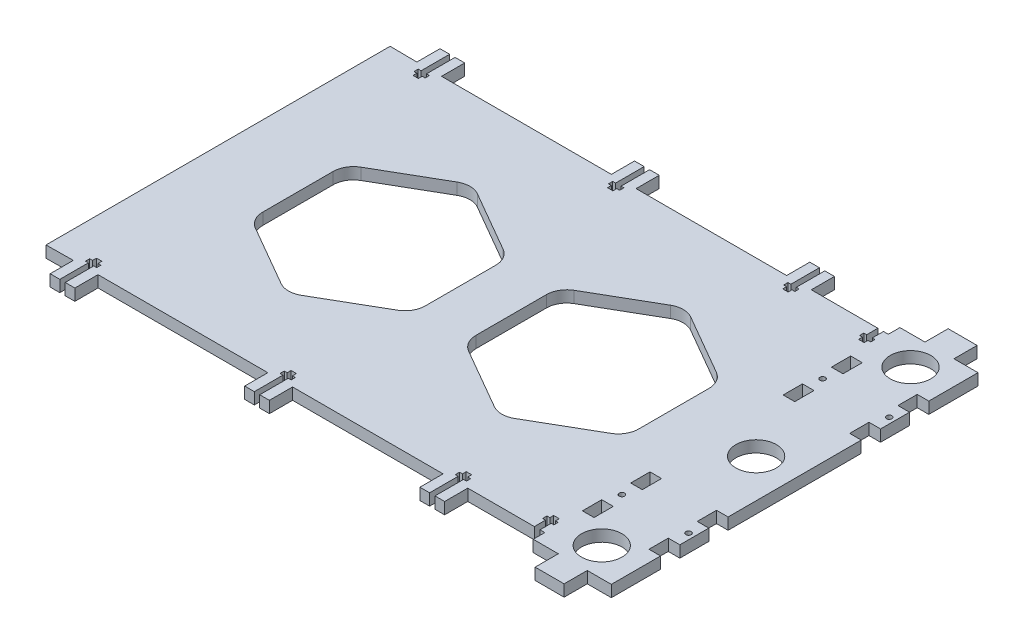
SolidWorks part; units mm, degrees
ref_plane "Спереди" through (0, 0, 0) normal (0, 0, 1) x (1, 0, 0)
ref_plane "Сверху" through (0, 0, 0) normal (0, 1, 0) x (1, 0, 0)
ref_plane "Справа" through (0, 0, 0) normal (1, 0, 0) x (0, 0, -1)
sketch "Эскиз1" plane through (0, 0, 0) normal (0, 1, 0) x (1, 0, 0)
  line L32 (-23.9169, 26.9382) -> (-55.4959, 45.1703)
  line L33 (-66.0222, 45.1703) -> (-97.6012, 26.9382)
  line L34 (-102.8643, 17.8222) -> (-102.8643, -0.4099)
  line L37 (-18.6538, -18.6421) -> (-18.6538, 17.8222)
  line L40 (91.8726, -0.4099) -> (91.8726, 17.8222)
  line L41 (86.6094, 26.9382) -> (55.0304, 45.1703)
  line L42 (44.5041, 45.1703) -> (12.9252, 26.9382)
  line L43 (7.662, 17.8222) -> (7.662, -18.6421)
  line L188 (154.5041, 128.5638) -> (154.5041, -125.2674) construction
  line L189 (175.6449, -0.4099) -> (-201.3479, -0.4099) construction
  line L190 (169.6988, 94.5901) -> (-201.3479, 94.5901) construction
  line L191 (168.2514, -95.4099) -> (-202.7953, -95.4099) construction
  line L192 (169.6988, 106.5901) -> (89.704, 106.5901) construction
  line L193 (-117.4736, -101.4099) -> (-117.4736, -89.4099)
  line L194 (108.4192, -125.2328) -> (108.4192, 116.6247) construction
  line L195 (134.5357, 79.5901) -> (134.5357, 90.0901) construction
  line L196 (134.5357, 128.5638) -> (134.5357, -125.2674) construction
  line L197 (148.5041, 128.5638) -> (148.5041, -125.2674) construction
  line L198 (169.6988, 69.0901) -> (102.787, 69.0901) construction
  line L199 (120.0357, -95.4099) -> (114.0357, -95.4099)
  line L200 (169.6988, 59.0901) -> (102.787, 59.0901) construction
  line L201 (102.787, 44.0901) -> (169.6988, 44.0901) construction
  line L202 (102.787, 34.0901) -> (169.6988, 34.0901) construction
  line L203 (-122.4736, -101.4099) -> (-117.4736, -101.4099)
  line L204 (-130.2736, -101.4099) -> (-130.2736, -89.4099)
  line L205 (-125.2736, -101.4099) -> (-130.2736, -101.4099)
  line L206 (-126.7736, -86.6099) -> (-125.2736, -86.6099)
  line L207 (154.5041, 69.0901) -> (148.5041, 69.0901)
  line L208 (148.5041, 69.0901) -> (148.5041, 59.0901)
  line L209 (148.5041, 59.0901) -> (154.5041, 59.0901)
  line L210 (154.5041, 44.0901) -> (148.5041, 44.0901)
  line L211 (148.5041, 44.0901) -> (148.5041, 34.0901)
  line L212 (148.5041, 34.0901) -> (154.5041, 34.0901)
  line L213 (151.5041, 128.5638) -> (151.5041, -125.2674) construction
  line L214 (169.6988, 51.5901) -> (102.787, 51.5901) construction
  line L215 (-126.7736, -84.4099) -> (-126.7736, -86.6099)
  line L223 (154.5041, -34.9099) -> (154.5041, 34.0901)
  line L224 (154.5041, 44.0901) -> (154.5041, 59.0901)
  line L225 (154.5041, 69.0901) -> (154.5041, 94.5901)
  line L227 (142.0357, 94.5901) -> (142.0357, 106.5901)
  line L228 (142.0357, 106.5901) -> (127.0357, 106.5901)
  line L229 (127.0357, 106.5901) -> (127.0357, 94.5901)
  line L230 (142.0357, 94.5901) -> (154.5041, 94.5901)
  line L231 (124.0357, 116.5901) -> (124.0357, -125.2674) construction
  line L232 (120.0357, 116.5901) -> (120.0357, -125.2674) construction
  line L233 (114.0357, 116.5901) -> (114.0357, -125.2674) construction
  line L234 (169.6988, 88.5901) -> (114.0357, 88.5901) construction
  line L236 (120.0357, 94.5901) -> (127.0357, 94.5901)
  line L238 (-24.4736, 100.5895) -> (-24.4736, 85.7895)
  line L239 (116.9781, 116.5901) -> (116.9781, -125.2674) construction
  line L240 (114.0357, 69.0901) -> (120.0357, 69.0901)
  line L241 (114.0357, 69.0901) -> (114.0357, 59.0901)
  line L242 (114.0357, 59.0901) -> (120.0357, 59.0901)
  line L243 (120.0357, 69.0901) -> (120.0357, 59.0901)
  line L244 (114.0357, 44.0901) -> (120.0357, 44.0901)
  line L245 (114.0357, 44.0901) -> (114.0357, 34.0901)
  line L246 (114.0357, 34.0901) -> (120.0357, 34.0901)
  line L247 (120.0357, 44.0901) -> (120.0357, 34.0901)
  line L248 (-125.2736, -84.4099) -> (-126.7736, -84.4099)
  line L257 (-125.2736, -82.4099) -> (-125.2736, -84.4099)
  line L258 (-122.4736, -82.4099) -> (-125.2736, -82.4099)
  line L259 (-122.4736, -84.4099) -> (-122.4736, -82.4099)
  line L260 (-120.9736, -84.4099) -> (-122.4736, -84.4099)
  line L261 (-120.9736, -86.6099) -> (-120.9736, -84.4099)
  line L262 (-122.4736, -86.6099) -> (-120.9736, -86.6099)
  line L263 (-130.2736, -89.4099) -> (-144.2736, -89.5669)
  line L264 (-16.6736, -101.4094) -> (-16.6736, -89.4099)
  line L265 (112.9264, 107.7365) -> (112.9264, -92.2635) construction
  line L266 (111.5357, 107.7365) -> (111.5357, -92.2635) construction
  line L267 (108.6264, 107.7365) -> (108.6264, -92.2635) construction
  line L268 (107.1264, 107.7365) -> (107.1264, -92.2635) construction
  line L269 (-21.6736, -101.4094) -> (-16.6736, -101.4094)
  line L270 (127.0357, -95.4099) -> (120.0357, -95.4099)
  line L271 (-29.4736, -101.4094) -> (-29.4736, -89.4094)
  line L272 (-24.4736, -101.4094) -> (-29.4736, -101.4094)
  line L273 (-117.4736, -89.4099) -> (-29.4736, -89.4094)
  line L274 (-21.6736, -86.6094) -> (-21.6736, -101.4094)
  line L275 (-25.9736, -86.6094) -> (-24.4736, -86.6094)
  line L276 (-25.9736, -84.4094) -> (-25.9736, -86.6094)
  line L277 (-24.4736, -84.4094) -> (-25.9736, -84.4094)
  line L278 (-24.4736, -82.4094) -> (-24.4736, -84.4094)
  line L279 (-21.6736, -82.4094) -> (-24.4736, -82.4094)
  line L280 (-21.6736, -84.4094) -> (-21.6736, -82.4094)
  line L281 (-20.1736, -84.4094) -> (-21.6736, -84.4094)
  line L282 (121.9861, 78.5901) -> (101.737, 78.5901) construction
  line L283 (121.9861, 80.5901) -> (101.737, 80.5901) construction
  line L284 (121.9861, 82.7901) -> (101.737, 82.7901) construction
  line L285 (111.5357, 88.5901) -> (111.5357, 82.7901)
  line L286 (111.5357, 82.7901) -> (112.9264, 82.7901)
  line L287 (112.9264, 82.7901) -> (112.9264, 80.5901)
  line L288 (112.9264, 80.5901) -> (111.5357, 80.5901)
  line L289 (111.5357, 80.5901) -> (111.5357, 78.5901)
  line L290 (111.5357, 78.5901) -> (108.6264, 78.5901)
  line L291 (108.6264, 78.5901) -> (108.6264, 80.5901)
  line L292 (108.6264, 80.5901) -> (107.1264, 80.5901)
  line L293 (107.1264, 80.5901) -> (107.1264, 82.7901)
  line L294 (107.1264, 82.7901) -> (108.6264, 82.7901)
  line L295 (108.6264, 82.7901) -> (108.6264, 88.5901)
  line L296 (108.6264, 88.5901) -> (74.1264, 88.5901)
  line L297 (169.6988, 100.5901) -> (-201.3479, 100.5901) construction
  line L298 (70.6264, 45.1703) -> (70.6264, 137.9979) construction
  line L299 (-23.0736, 45.1703) -> (-23.0736, 137.9979) construction
  line L300 (-123.8736, 137.9979) -> (-123.8736, 45.1703) construction
  line L301 (75.3218, 85.7901) -> (58.936, 85.7901) construction
  line L302 (75.3218, 83.5901) -> (58.936, 83.5901) construction
  line L303 (75.3218, 81.5901) -> (58.936, 81.5901) construction
  line L304 (69.1264, 137.9979) -> (69.1264, 45.1703) construction
  line L305 (66.3264, 137.819) -> (66.3264, 44.9915) construction
  line L306 (64.8264, 137.819) -> (64.8264, 44.9915) construction
  line L307 (66.3264, 100.5901) -> (66.3264, 85.7901)
  line L308 (69.1264, 85.7901) -> (70.6264, 85.7901)
  line L309 (70.6264, 85.7901) -> (70.6264, 83.5901)
  line L310 (70.6264, 83.5901) -> (69.1264, 83.5901)
  line L311 (69.1264, 83.5901) -> (69.1264, 81.5901)
  line L312 (69.1264, 81.5901) -> (66.3264, 81.5901)
  line L313 (66.3264, 81.5901) -> (66.3264, 83.5901)
  line L314 (66.3264, 83.5901) -> (64.8264, 83.5901)
  line L315 (64.8264, 83.5901) -> (64.8264, 85.7901)
  line L316 (64.8264, 85.7901) -> (66.3264, 85.7901)
  line L317 (69.1264, 100.5901) -> (69.1264, 85.7901)
  line L318 (-125.2736, 100.5901) -> (-125.2736, 85.7901)
  line L319 (66.3264, 100.5901) -> (61.3264, 100.5901)
  line L320 (61.3264, 100.5901) -> (61.3264, 88.5901)
  line L321 (-122.4736, 100.5901) -> (-122.4736, 85.7901)
  line L322 (69.1264, 100.5901) -> (74.1264, 100.5901)
  line L323 (74.1264, 100.5901) -> (74.1264, 88.5901)
  line L324 (61.3264, 88.5901) -> (-16.6736, 88.5901)
  line L325 (-21.6736, 85.7895) -> (-20.1736, 85.7895)
  line L326 (-20.1736, 85.7895) -> (-20.1736, 83.5895)
  line L327 (-20.1736, 83.5895) -> (-21.6736, 83.5895)
  line L328 (-21.6736, 83.5895) -> (-21.6736, 81.5895)
  line L329 (-21.6736, 81.5895) -> (-24.4736, 81.5895)
  line L330 (-24.4736, 81.5895) -> (-24.4736, 83.5895)
  line L331 (-24.4736, 83.5895) -> (-25.9736, 83.5895)
  line L332 (-25.9736, 83.5895) -> (-25.9736, 85.7895)
  line L333 (-25.9736, 85.7895) -> (-24.4736, 85.7895)
  line L334 (-21.6736, 85.7895) -> (-21.6736, 100.5895)
  line L335 (-117.4736, 88.5901) -> (-29.4736, 88.5895)
  line L336 (-24.4736, 100.5895) -> (-29.4736, 100.5895)
  line L337 (-29.4736, 100.5895) -> (-29.4736, 88.5895)
  line L338 (-144.2736, 137.9979) -> (-144.2736, 39.4961) construction
  line L339 (-21.6736, 100.5895) -> (-16.6736, 100.5895)
  line L340 (-16.6736, 100.5895) -> (-16.6736, 88.5901)
  line L341 (-130.2736, 88.5901) -> (-144.2736, 88.747)
  line L343 (-122.4736, 85.7901) -> (-120.9736, 85.7901)
  line L344 (-120.9736, 85.7901) -> (-120.9736, 83.5901)
  line L345 (-120.9736, 83.5901) -> (-122.4736, 83.5901)
  line L346 (-122.4736, 83.5901) -> (-122.4736, 81.5901)
  line L347 (-122.4736, 81.5901) -> (-125.2736, 81.5901)
  line L348 (-125.2736, 81.5901) -> (-125.2736, 83.5901)
  line L349 (-125.2736, 83.5901) -> (-126.7736, 83.5901)
  line L350 (-126.7736, 83.5901) -> (-126.7736, 85.7901)
  line L351 (-126.7736, 85.7901) -> (-125.2736, 85.7901)
  line L352 (-20.1736, -86.6094) -> (-20.1736, -84.4094)
  line L353 (-21.6736, -86.6094) -> (-20.1736, -86.6094)
  line L354 (-125.2736, 100.5901) -> (-130.2736, 100.5901)
  line L355 (-130.2736, 100.5901) -> (-130.2736, 88.5901)
  line L356 (61.3264, -89.4099) -> (-16.6736, -89.4099)
  line L357 (-122.4736, 100.5901) -> (-117.4736, 100.5901)
  line L358 (-117.4736, 100.5901) -> (-117.4736, 88.5901)
  line L359 (74.1264, -101.4099) -> (74.1264, -89.4099)
  line L360 (69.1264, -101.4099) -> (74.1264, -101.4099)
  line L361 (-122.4736, -101.4099) -> (-122.4736, -86.6099)
  line L362 (61.3264, -101.4099) -> (61.3264, -89.4099)
  line L363 (66.3264, -101.4099) -> (61.3264, -101.4099)
  line L364 (-125.2736, -101.4099) -> (-125.2736, -86.6099)
  line L365 (69.1264, -101.4099) -> (69.1264, -86.6099)
  line L366 (64.8264, -86.6099) -> (66.3264, -86.6099)
  line L367 (64.8264, -84.4099) -> (64.8264, -86.6099)
  line L368 (66.3264, -84.4099) -> (64.8264, -84.4099)
  line L369 (66.3264, -82.4099) -> (66.3264, -84.4099)
  line L370 (69.1264, -82.4099) -> (66.3264, -82.4099)
  line L371 (69.1264, -84.4099) -> (69.1264, -82.4099)
  line L372 (70.6264, -84.4099) -> (69.1264, -84.4099)
  line L373 (70.6264, -86.6099) -> (70.6264, -84.4099)
  line L374 (69.1264, -86.6099) -> (70.6264, -86.6099)
  line L375 (66.3264, -101.4099) -> (66.3264, -86.6099)
  line L376 (-144.2736, 88.747) -> (-144.2736, -89.5669)
  line L377 (114.0357, -95.4099) -> (114.0357, -89.4099)
  line L378 (114.0357, -89.4099) -> (111.5357, -89.4099)
  line L379 (114.0357, 88.5901) -> (114.0357, 94.5901)
  line L380 (114.0357, 94.5901) -> (120.0357, 94.5901)
  line L381 (114.0357, 88.5901) -> (111.5357, 88.5901)
  line L385 (108.6264, -89.4099) -> (74.1264, -89.4099)
  line L386 (108.6264, -83.6099) -> (108.6264, -89.4099)
  line L387 (107.1264, -83.6099) -> (108.6264, -83.6099)
  line L388 (107.1264, -81.4099) -> (107.1264, -83.6099)
  line L389 (108.6264, -81.4099) -> (107.1264, -81.4099)
  line L390 (108.6264, -79.4099) -> (108.6264, -81.4099)
  line L391 (111.5357, -79.4099) -> (108.6264, -79.4099)
  line L392 (111.5357, -81.4099) -> (111.5357, -79.4099)
  line L393 (112.9264, -81.4099) -> (111.5357, -81.4099)
  line L394 (112.9264, -83.6099) -> (112.9264, -81.4099)
  line L395 (111.5357, -83.6099) -> (112.9264, -83.6099)
  line L396 (111.5357, -89.4099) -> (111.5357, -83.6099)
  line L400 (120.0357, -44.9099) -> (120.0357, -34.9099)
  line L401 (114.0357, -34.9099) -> (120.0357, -34.9099)
  line L402 (114.0357, -44.9099) -> (114.0357, -34.9099)
  line L403 (114.0357, -44.9099) -> (120.0357, -44.9099)
  line L404 (120.0357, -69.9099) -> (120.0357, -59.9099)
  line L405 (114.0357, -59.9099) -> (120.0357, -59.9099)
  line L406 (114.0357, -69.9099) -> (114.0357, -59.9099)
  line L407 (114.0357, -69.9099) -> (120.0357, -69.9099)
  line L408 (-24.4736, -101.4094) -> (-24.4736, -86.6094)
  line L413 (142.0357, -95.4099) -> (154.5041, -95.4099)
  line L414 (127.0357, -107.4099) -> (127.0357, -95.4099)
  line L415 (142.0357, -107.4099) -> (127.0357, -107.4099)
  line L416 (142.0357, -95.4099) -> (142.0357, -107.4099)
  line L417 (154.5041, -69.9099) -> (154.5041, -95.4099)
  line L418 (154.5041, -44.9099) -> (154.5041, -59.9099)
  line L420 (148.5041, -34.9099) -> (154.5041, -34.9099)
  line L421 (148.5041, -44.9099) -> (148.5041, -34.9099)
  line L422 (154.5041, -44.9099) -> (148.5041, -44.9099)
  line L423 (148.5041, -59.9099) -> (154.5041, -59.9099)
  line L424 (148.5041, -69.9099) -> (148.5041, -59.9099)
  line L425 (154.5041, -69.9099) -> (148.5041, -69.9099)
  line L433 (44.5041, -45.9902) -> (12.9252, -27.7581)
  line L434 (86.6094, -27.7581) -> (55.0304, -45.9902)
  line L435 (91.8726, -0.4099) -> (91.8726, -18.6421)
  line L436 (-102.8643, -18.6421) -> (-102.8643, -0.4099)
  line L437 (-66.0222, -45.9902) -> (-97.6012, -27.7581)
  line L438 (-23.9169, -27.7581) -> (-55.4959, -45.9902)
  circle A3 centre (134.5357, 79.5901) radius 10.5
  circle A14 centre (134.5357, -0.4099) radius 10.5
  arc A15 (-18.6538, 17.8222) -> (-23.9169, 26.9382) centre (-29.1801, 17.8222) ccw
  arc A16 (-55.4959, 45.1703) -> (-66.0222, 45.1703) centre (-60.7591, 36.0543) ccw
  arc A17 (-97.6012, 26.9382) -> (-102.8643, 17.8222) centre (-92.338, 17.8222) ccw
  arc A24 (91.8726, 17.8222) -> (86.6094, 26.9382) centre (81.3462, 17.8222) ccw
  arc A25 (55.0304, 45.1703) -> (44.5041, 45.1703) centre (49.7673, 36.0543) ccw
  arc A26 (12.9252, 26.9382) -> (7.662, 17.8222) centre (18.1883, 17.8222) ccw
  circle A31 centre (151.5041, 51.5901) radius 1.4
  circle A33 centre (116.9781, 51.5901) radius 1.4
  circle A35 centre (116.9781, -52.4099) radius 1.4
  circle A36 centre (151.5041, -52.4099) radius 1.4
  arc A37 (12.9252, -27.7581) -> (7.662, -18.6421) centre (18.1883, -18.6421) cw
  arc A38 (55.0304, -45.9902) -> (44.5041, -45.9902) centre (49.7673, -36.8742) cw
  arc A39 (91.8726, -18.6421) -> (86.6094, -27.7581) centre (81.3462, -18.6421) cw
  arc A40 (-97.6012, -27.7581) -> (-102.8643, -18.6421) centre (-92.338, -18.6421) cw
  arc A41 (-55.4959, -45.9902) -> (-66.0222, -45.9902) centre (-60.7591, -36.8742) cw
  arc A42 (-18.6538, -18.6421) -> (-23.9169, -27.7581) centre (-29.1801, -18.6421) cw
  circle A43 centre (134.5357, -80.4099) radius 10.5
  point P26 (-18.6538, -0.4099)
  point P111 (-144.2736, -0.4099)
  point P228 (154.5041, -0.4099)
  point P246 (7.662, -0.4099)
  point P314 (-123.8736, 81.5901)
  point P326 (-23.0736, 81.5895)
  dimension "D1" = 21
  dimension "D4" = 80
  dimension "D6" = 95
  dimension "D19" = 2.8
  dimension "D24" = 4
  dimension "D27" = 2.8
  dimension "D8" = 12
  dimension "D11" = 10
  dimension "D12" = 10
  dimension "D13" = 15
  dimension "D17" = 3
  dimension "D18" = 7.5
  dimension "D22" = 7.5
  dimension "D23" = 15
  dimension "D25" = 6
  dimension "D26" = 6
  dimension "D32" = 12
  dimension "D33" = 38
  dimension "D34" = 1.5
  dimension "D35" = 2.8
  dimension "D36" = 1.5
  dimension "D37" = 7
  dimension "D38" = 2
  dimension "D39" = 2.2
  dimension "D40" = 5
  dimension "D41" = 5
  dimension "D42" = 5
  dimension "D43" = 2.8
  dimension "D44" = 5
  dimension "D45" = 88
  dimension "D46" = 78
  dimension "D47" = 100.8
  dimension "D48" = 84.4
  dimension "D49" = 5
  dimension "D50" = 2.8
  dimension "D51" = 5
  dimension "D52" = 14
extrude "Бобышка-Вытянуть1" add sketch "Эскиз1" along normal blind 6
